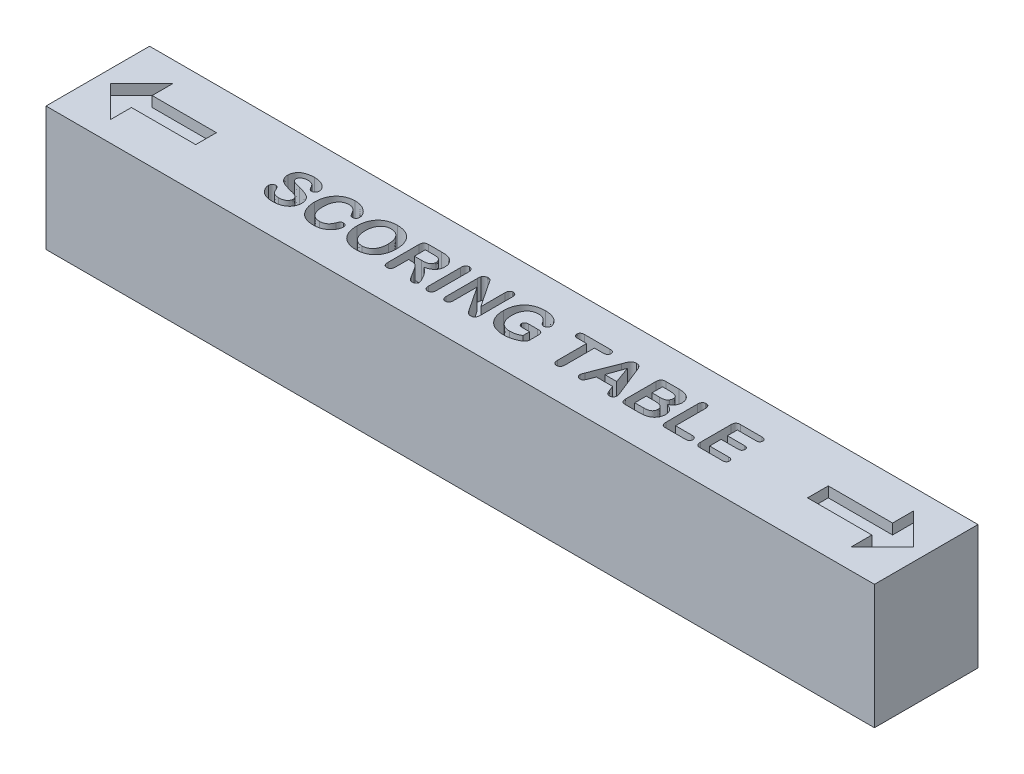
SolidWorks part; units mm, degrees
ref_plane "Front Plane" through (0, 0, 0) normal (0, 0, 1) x (1, 0, 0)
ref_plane "Top Plane" through (0, 0, 0) normal (0, 1, 0) x (1, 0, 0)
ref_plane "Right Plane" through (0, 0, 0) normal (1, 0, 0) x (0, 0, -1)
sketch "Sketch1" plane through (0, 0, 0) normal (0, 1, 0) x (1, 0, 0)
  line L1 (3048, 381) -> (-3048, 381)
  line L2 (3048, 381) -> (3048, -381)
  line L3 (3048, -381) -> (-3048, -381)
  line L4 (-3048, 381) -> (-3048, -381)
  line L5 (3048, 381) -> (-3048, -381) construction
  line L6 (3048, -381) -> (-3048, 381) construction
  point P0 (0, 0)
  dimension "D1" = 6096
  dimension "D2" = 762
extrude "Boss-Extrude1" add sketch "Sketch1" along normal blind 914.4
sketch "Sketch2" plane through (0, 914.4, 0) normal (0, 1, 0) x (1, 0, 0)
  line L0 (-3048, -152.4) -> (3048, -152.4) construction
  line L3 (-3048, 381) -> (-3048, -381) construction
  line L4 (3048, -381) -> (3048, 381) construction
  line L5 (-3048, -381) -> (3048, -381) construction
  text T0 "SCORING TABLE" font "Arial Rounded MT Bold" height in points 1200
  dimension "D1" = 228.6
extrude "Cut-Extrude1" cut sketch "Sketch2" against normal blind 152.4
sketch "Sketch3" plane through (0, 914.4, 0) normal (0, 1, 0) x (1, 0, 0)
  line L0 (2724.15, 76.2) -> (2724.15, 231.775)
  line L1 (2251.075, 76.2) -> (2724.15, 76.2)
  line L2 (2251.075, 76.2) -> (2251.075, -76.2)
  line L3 (2251.075, -76.2) -> (2724.15, -76.2)
  line L4 (2724.15, 76.2) -> (2724.15, -76.2) construction
  line L5 (2724.15, 231.775) -> (2955.925, 0)
  line L6 (2955.925, 0) -> (2724.15, -231.775)
  line L7 (2724.15, -231.775) -> (2724.15, -76.2)
  line L8 (3048, -381) -> (3048, 381) construction
  point P7 (2724.15, 0)
  point P10 (3048, 0)
  dimension "D1" = 704.85
  dimension "D2" = 473.075
  dimension "D3" = 152.4
  dimension "D4" = 92.075
extrude "Cut-Extrude2" cut sketch "Sketch3" against normal blind 76.2
mirror "Mirror1" about plane through (0, 0, 0) normal (1, 0, 0) of "Cut-Extrude2"
